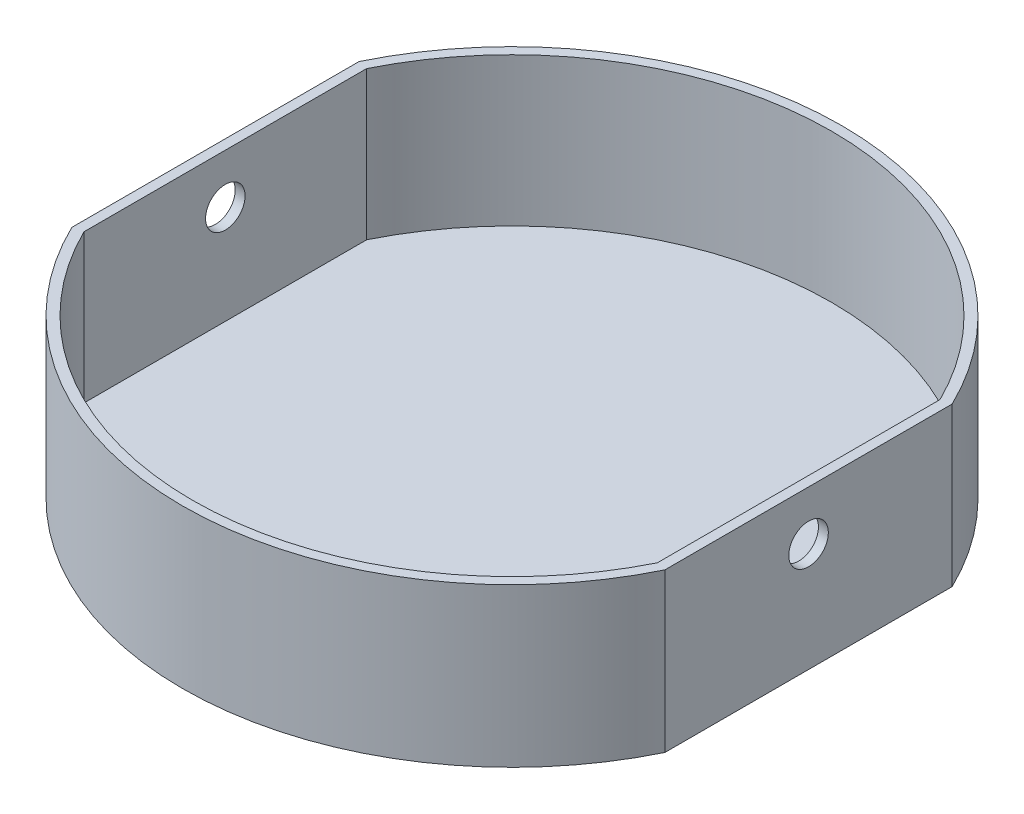
SolidWorks part; units mm, degrees
ref_plane "Front Plane" through (0, 0, 0) normal (0, 0, 1) x (1, 0, 0)
ref_plane "Top Plane" through (0, 0, 0) normal (0, 1, 0) x (1, 0, 0)
ref_plane "Right Plane" through (0, 0, 0) normal (1, 0, 0) x (0, 0, -1)
sketch "Sketch1" plane through (0, 0, 0) normal (0, 1, 0) x (1, 0, 0)
  circle A0 centre (0, 0) radius 100
extrude "Boss-Extrude2" add sketch "Sketch1" along normal blind 3
sketch "Sketch5" plane through (0, 3, 0) normal (0, 1, 0) x (1, 0, 0)
  line L0 (0, 0) -> (90, 0)
  line L1 (90, 0) -> (90, 43.589)
  line L3 (90, 43.589) -> (87, 43.589)
  line L4 (90, 43.589) -> (90, -43.411)
  line L5 (90, -43.411) -> (87, -43.411)
  line L6 (87, 43.589) -> (87, -43.411)
  circle A0 centre (0, 0) radius 100 construction
  dimension "D1" = 87
  dimension "D2" = 3
extrude "Boss-Extrude5" add sketch "Sketch5" along normal blind 45 contours L4 L5 L6 L3
sketch "Sketch8" plane through (0, 3, 0) normal (0, 1, 0) x (1, 0, 0)
  line L0 (0, 0) -> (-90, 0)
  line L1 (-90, 0) -> (-90, 43.589)
  line L3 (-90, 43.589) -> (-87, 43.589)
  line L4 (-90, 43.589) -> (-90, -43.411)
  line L5 (-90, -43.411) -> (-87, -43.411)
  line L6 (-87, 43.589) -> (-87, -43.411)
  circle A0 centre (0, 0) radius 100 construction
  dimension "D1" = 87
  dimension "D2" = 3
extrude "Boss-Extrude6" add sketch "Sketch8" along normal blind 45 contours L3 L6 L5 L4
sketch "Sketch9" plane through (0, 3, 0) normal (0, 1, 0) x (1, 0, 0)
  line L0 (90, 43.589) -> (90, -43.411) construction
  line L1 (90, 43.589) -> (113.7197, 43.589)
  line L2 (90, 43.589) -> (90, -50.7128)
  line L3 (90, -50.7128) -> (113.7197, -50.7128)
  line L4 (113.7197, 43.589) -> (113.7197, -50.7128)
  arc A0 (-90, 43.589) -> (90, 43.589) centre (0, 0) ccw construction
extrude "Cut-Extrude2" cut sketch "Sketch9" against normal blind 45
sketch "Sketch10" plane through (0, 3, 0) normal (0, 1, 0) x (1, 0, 0)
  line L1 (-90, -43.411) -> (-113.9697, -43.411)
  line L2 (-90, -43.411) -> (-90, 49.0364)
  line L3 (-90, 49.0364) -> (-113.9697, 49.0364)
  line L4 (-113.9697, -43.411) -> (-113.9697, 49.0364)
extrude "Cut-Extrude3" cut sketch "Sketch10" against normal blind 45
sketch "Sketch11" plane through (-90, 0, 0) normal (-1, 0, 0) x (0, 0, 1)
  line L0 (0, 0) -> (0, 33)
  circle A0 centre (0, 33) radius 6
extrude "Cut-Extrude4" cut sketch "Sketch11" against normal blind 45
sketch "Sketch12" plane through (90, 0, 0) normal (1, 0, 0) x (0, 0, -1)
  line L0 (0, 0) -> (0, 33)
  circle A0 centre (0, 33) radius 6
extrude "Cut-Extrude5" cut sketch "Sketch12" against normal blind 45 contours A0
sketch "Sketch14" plane through (0, 3, 0) normal (0, 1, 0) x (1, 0, 0)
  line L8 (-90, -43.411) -> (-90.086, -43.411)
  line L9 (90, -43.589) -> (90, -43.411)
  line L10 (90, -43.411) -> (87, -43.411)
  line L11 (87, -43.411) -> (87, 43.589)
  line L12 (87, 43.589) -> (90, 43.589)
  line L13 (-90, 43.589) -> (-87, 43.589)
  line L14 (-87, 43.589) -> (-87, -43.411)
  line L15 (-87, -43.411) -> (-90, -43.411)
  line L16 (-90, -43.411) -> (-90.086, -43.411)
  line L17 (90, -43.589) -> (90, -43.411)
  line L18 (90, -43.411) -> (87, -43.411)
  line L19 (87, -43.411) -> (87, 43.589)
  line L20 (87, 43.589) -> (90, 43.589)
  line L21 (-90, 43.589) -> (-87, 43.589)
  line L22 (-87, 43.589) -> (-87, -43.411)
  line L23 (-87, -43.411) -> (-90, -43.411)
  arc A0 (-90, 43.589) -> (90, 43.589) centre (0, 0) cw
  arc A3 (-90.086, -43.411) -> (90, -43.589) centre (0, 0) ccw
  arc A4 (90, 43.589) -> (-90, 43.589) centre (0, 0) ccw
  arc A5 (-90.086, -43.411) -> (90, -43.589) centre (0, 0) ccw
  dimension "D1" = 0
extrude "Boss-Extrude7" add sketch "Sketch14" along normal blind 45
sketch3d "3DSketch1"
  line L0 (-87, 48, -42.8952) -> (-87, 48, 42.8952)
  line L1 (87, 48, -42.8952) -> (87, 48, 42.8952)
  line L2 (-87, 48, -42.8952) -> (-87, 48, 42.8952)
  line L3 (87, 48, -42.8952) -> (87, 48, 42.8952)
  arc A0 (-87, 48, 42.8952) -> (87, 48, 42.8952) centre (0, 48, 0) ccw
  arc A1 (87, 48, -42.8952) -> (-87, 48, -42.8952) centre (0, 48, 0) ccw
  arc A2 (-87, 48, 42.8952) -> (87, 48, 42.8952) centre (0, 48, 0) ccw
  arc A3 (87, 48, -42.8952) -> (-87, 48, -42.8952) centre (0, 48, 0) ccw
  point P4 (0, 145, 0)
  point P7 (0, 145, 0)
  point P8 (0, 145, 0)
  point P9 (0, 145, 0)
  dimension "D1" = 3
extrude "Cut-Extrude6" cut sketch "3DSketch1" along a picked direction on the side of the normal blind 45 contours L2 A2 L3 A3
